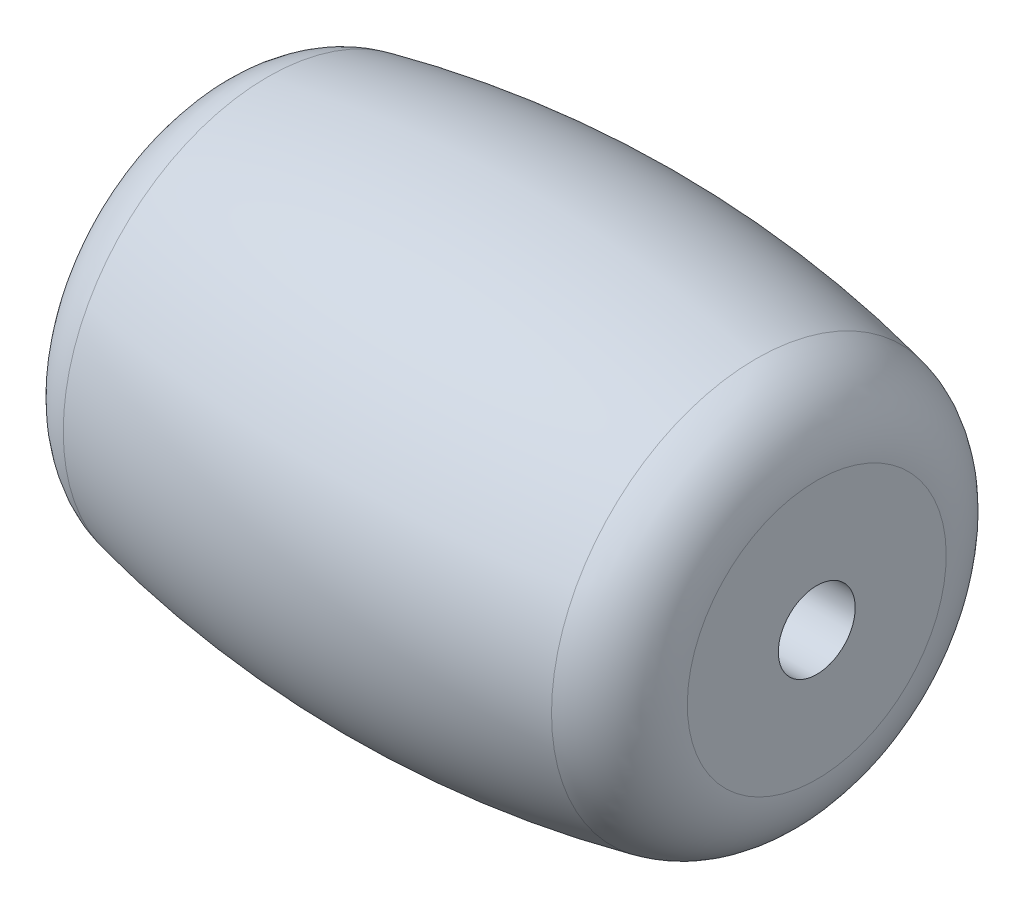
SolidWorks part; units mm, degrees
ref_plane "Piano frontale" through (0, 0, 0) normal (0, 0, 1) x (1, 0, 0)
ref_plane "Piano superiore" through (0, 0, 0) normal (0, 1, 0) x (1, 0, 0)
ref_plane "Piano destro" through (0, 0, 0) normal (1, 0, 0) x (0, 0, -1)
ref_plane "Piano1" through (0, 0, 0) normal (0, 0, -1) x (-1, 0, 0)
sketch "Schizzo1" plane through (0, 0, 0) normal (0, 0, -1) x (-1, 0, 0)
  line L0 (-7.925, 4.9343) -> (-7.925, 0)
  line L1 (-7.925, 0) -> (7.925, 0)
  line L2 (7.925, 0) -> (7.925, 4.9343)
  line L3 (-7.925, 0) -> (7.925, 0) construction
  arc A0 (7.925, 4.9343) -> (-7.925, 4.9343) centre (0, -24) ccw
revolve "Rivoluzione1" add sketch "Schizzo1" angle 360 about L3
fillet "Raccordo1" radius 2 1 edges at (7.925, -4.9343, 0)
fillet "Raccordo2" radius 2 1 edges at (-7.925, -4.9343, 0)
hole_wizard "Foro Ø0.2 (0.2)-1" positions "Schizzo3" profile "Schizzo2" hole size "Ø0.2" standard "Ansi Metric"
sketch "Schizzo3" plane through (7.925, 0, 0) normal (1, 0, 0) x (0, 0, -1)
  point P0 (0, 0)
sketch "Schizzo2" plane through (7.925, 0, 0) normal (0, 1, 0) x (0, 0, -1)
  line L0 (0, 0) -> (0, 15.85)
  line L1 (0, 15.85) -> (1, 15.85)
  line L2 (1, 15.85) -> (1, 0)
  line L5 (1, 0) -> (0, 0)
  line L11 (0, -6.35) -> (0, 107.95) construction
  dimension "Thru Hole Dia." = 2
  dimension "Thru Hole Depth" = 15.85
